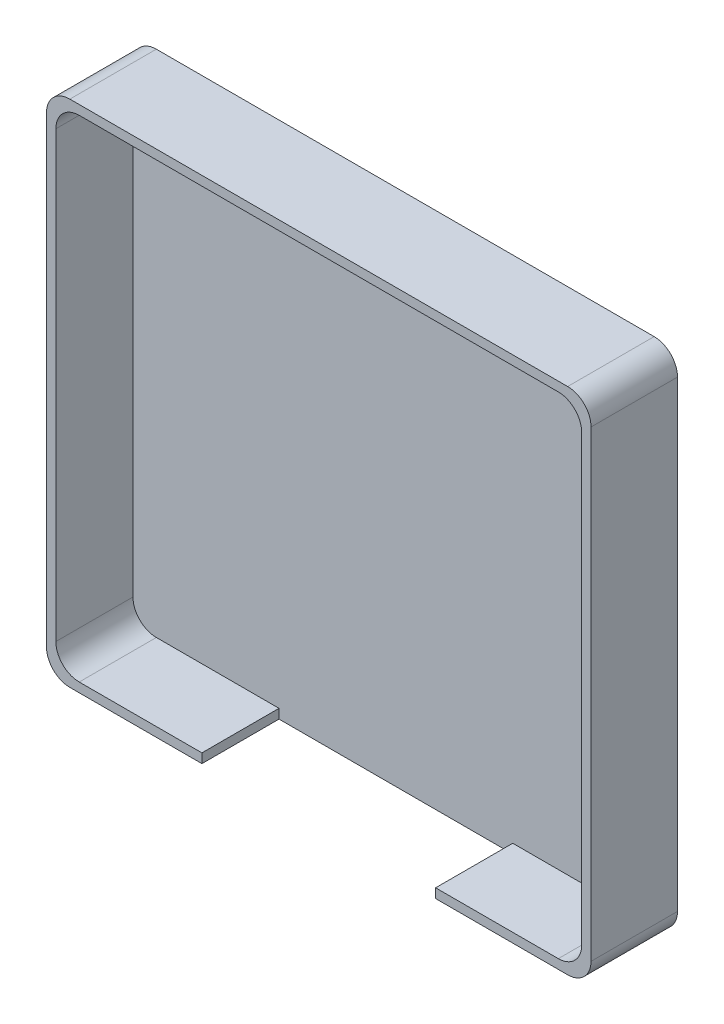
SolidWorks part; units mm, degrees
ref_plane "正面" through (0, 0, 0) normal (0, 0, 1) x (1, 0, 0)
ref_plane "平面" through (0, 0, 0) normal (0, 1, 0) x (1, 0, 0)
ref_plane "右側面" through (0, 0, 0) normal (1, 0, 0) x (0, 0, -1)
sketch "ｽｹｯﾁ1" plane through (0, 0, 0) normal (0, 0, 1) x (1, 0, 0)
  line L1 (-23.3, -21.8) -> (23.3, -21.8)
  line L2 (-23.3, -21.8) -> (-23.3, 21.8)
  line L3 (-23.3, 21.8) -> (23.3, 21.8)
  line L4 (23.3, -21.8) -> (23.3, 21.8)
  line L5 (-23.3, -21.8) -> (23.3, 21.8) construction
  line L6 (-23.3, 21.8) -> (23.3, -21.8) construction
  point P0 (0, 0)
  dimension "D1" = 46.6
  dimension "D2" = 43.6
extrude "ﾎﾞｽ - 押し出し1" add sketch "ｽｹｯﾁ1" along normal blind 7.4
sketch "ｽｹｯﾁ2" plane through (0, 0, 7.4) normal (0, 0, 1) x (1, 0, 0)
  line L0 (-23.3, 0) -> (23.3, 0) construction
  line L1 (-23.3, 21.8) -> (-23.3, -21.8) construction
  line L2 (23.3, -21.8) -> (23.3, 21.8) construction
  line L3 (0, 21.8) -> (0, -21.8) construction
  line L4 (23.3, 21.8) -> (-23.3, 21.8) construction
  line L5 (-23.3, -21.8) -> (23.3, -21.8) construction
  line L7 (22.5, -21) -> (-22.5, -21)
  line L8 (22.5, -21) -> (22.5, 21)
  line L9 (22.5, 21) -> (-22.5, 21)
  line L10 (-22.5, -21) -> (-22.5, 21)
  line L11 (22.5, -21) -> (-22.5, 21) construction
  line L12 (22.5, 21) -> (-22.5, -21) construction
  point P12 (0, 0)
  dimension "D1" = 45
  dimension "D2" = 42
extrude "ｶｯﾄ - 押し出し1" cut sketch "ｽｹｯﾁ2" against normal blind 6.6
sketch "ｽｹｯﾁ3" plane through (0, -21.8, 0) normal (0, -1, 0) x (-1, 0, 0)
  line L0 (23.3, -3.7) -> (-23.3, -3.7) construction
  line L1 (23.3, -7.4) -> (23.3, 0) construction
  line L2 (-23.3, -7.4) -> (-23.3, 0) construction
  line L3 (0, -7.4) -> (0, 0) construction
  line L4 (23.3, -7.4) -> (-23.3, -7.4) construction
  line L5 (23.3, 0) -> (-23.3, 0) construction
  line L6 (0, -7.4) -> (0, -0.8) construction
  line L7 (10, -7.4) -> (-10, -7.4)
  line L8 (10, -7.4) -> (10, -0.8)
  line L9 (10, -0.8) -> (-10, -0.8)
  line L10 (-10, -7.4) -> (-10, -0.8)
  dimension "D1" = 20
  dimension "D2" = 0.8
extrude "ｶｯﾄ - 押し出し3" cut sketch "ｽｹｯﾁ3" against normal up to next
fillet "ﾌｨﾚｯﾄ1" radius 2 8 edges at (23.3, 21.8, 3.7) (23.3, -21.8, 3.7) (-23.3, 21.8, 3.7) (-22.5, 21, 4.1) (-22.5, -21, 4.1) (-23.3, -21.8, 3.7) (22.5, -21, 4.1) (22.5, 21, 4.1)
